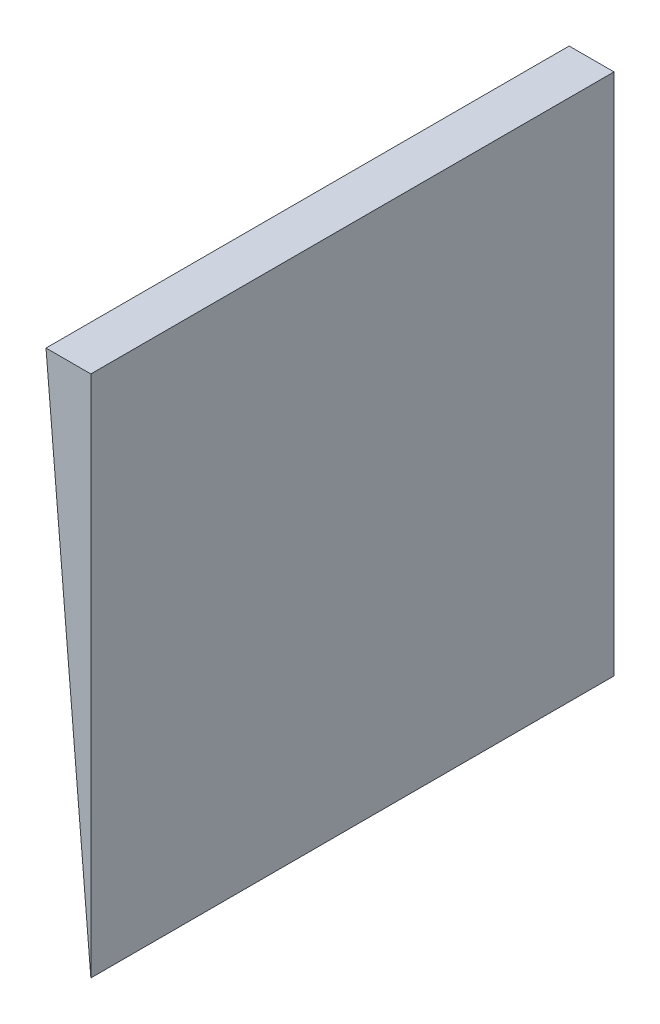
SolidWorks part; units mm, degrees
ref_plane "Front Plane" through (0, 0, 0) normal (0, 0, 1) x (1, 0, 0)
ref_plane "Top Plane" through (0, 0, 0) normal (0, 1, 0) x (1, 0, 0)
ref_plane "Right Plane" through (0, 0, 0) normal (1, 0, 0) x (0, 0, -1)
sketch "Sketch1" plane through (0, 0, 0) normal (0, 0, 1) x (1, 0, 0)
  line L0 (0, 0) -> (0, 35)
  line L1 (0, 35) -> (-3, 35)
  line L2 (-3, 35) -> (0, 0)
  dimension "D1" = 35
  dimension "D2" = 3
extrude "Boss-Extrude1" add sketch "Sketch1" along normal blind 35
